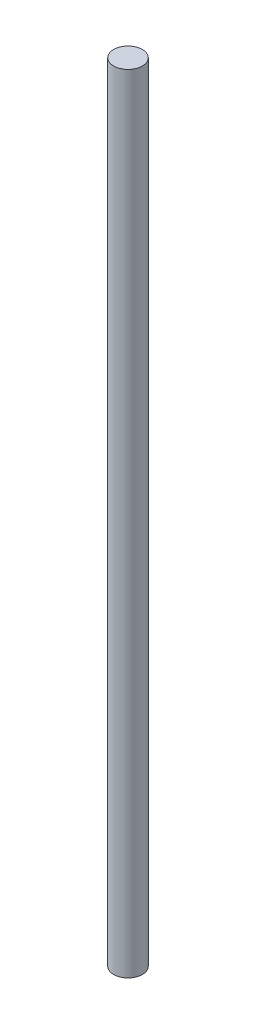
SolidWorks part; units mm, degrees
material "AISI 4340 Steel, annealed"
ref_plane "Front Plane" through (0, 0, 0) normal (0, 0, 1) x (1, 0, 0)
ref_plane "Top Plane" through (0, 0, 0) normal (0, 1, 0) x (1, 0, 0)
ref_plane "Right Plane" through (0, 0, 0) normal (1, 0, 0) x (0, 0, -1)
sketch "Sketch1" plane through (0, 0, 0) normal (0, 1, 0) x (1, 0, 0)
  circle A0 centre (0, 0) radius 5.5563
  dimension "D1" = 11.1125
extrude "Boss-Extrude1" add sketch "Sketch1" along normal mid plane 304.8
